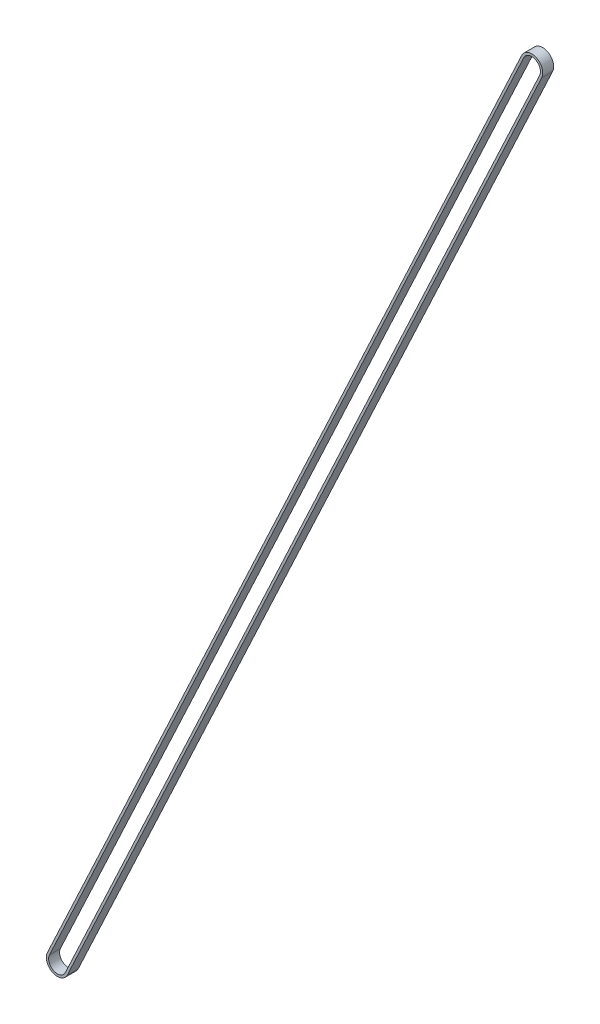
SolidWorks part; units mm, degrees
ref_plane "Front Plane" through (0, 0, 0) normal (0, 0, 1) x (1, 0, 0)
ref_plane "Top Plane" through (0, 0, 0) normal (0, 1, 0) x (1, 0, 0)
ref_plane "Right Plane" through (0, 0, 0) normal (1, 0, 0) x (0, 0, -1)
sketch "Sketch2" plane through (-2.1589, 13.6484, 0) normal (0, 0, 1) x (1, 0, 0)
  line L0 (0, 0) -> (1, 0) construction
  line L1 (0, 0) -> (0, 1) construction
  line L2 (17.3919, -8.134) -> (-806.8377, -1770.4911)
  line L3 (-841.6215, -1754.2232) -> (-17.3919, 8.134)
  arc A0 (-17.3919, 8.134) -> (17.3919, -8.134) centre (0, 0) cw
  arc A1 (-806.8377, -1770.4911) -> (-841.6215, -1754.2232) centre (-824.2296, -1762.3572) cw
extrude "Extrude-Thin1" add sketch "Sketch2" along normal blind 19 from surface thin
